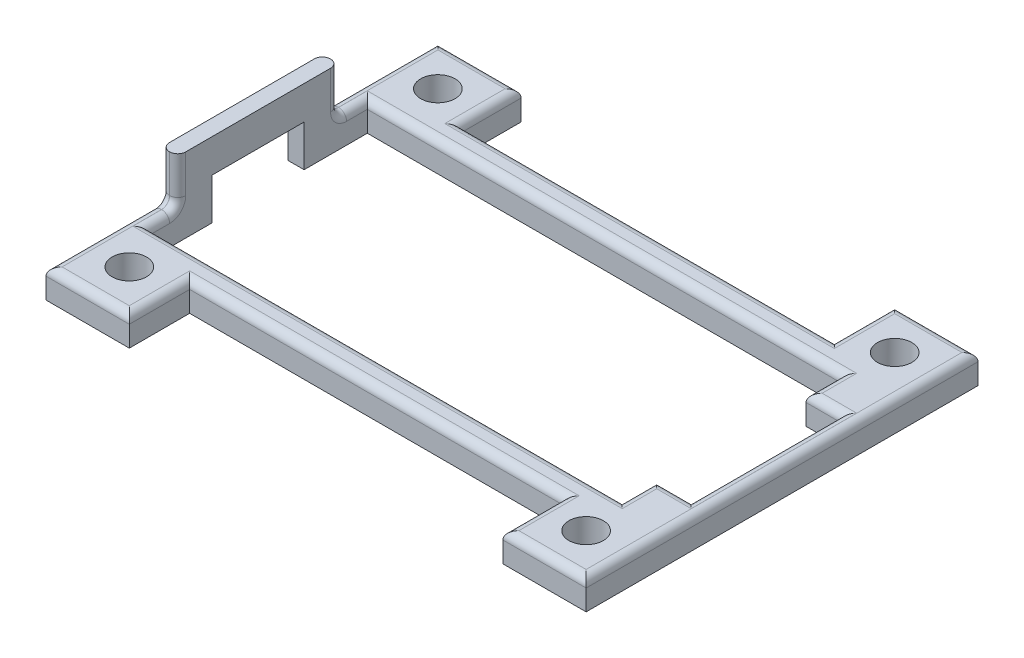
SolidWorks part; units mm, degrees
ref_plane "Front Plane" through (0, 0, 0) normal (0, 0, 1) x (1, 0, 0)
ref_plane "Top Plane" through (0, 0, 0) normal (0, 1, 0) x (1, 0, 0)
ref_plane "Right Plane" through (0, 0, 0) normal (1, 0, 0) x (0, 0, -1)
sketch "Sketch1" plane through (0, 0, 0) normal (0, 1, 0) x (1, 0, 0)
  line L1 (0, 0) -> (44.18, 0)
  line L2 (0, 0) -> (0, 19)
  line L3 (0, 19) -> (44.18, 19)
  line L4 (44.18, 0) -> (44.18, 19)
  line L5 (-1.41, 21.3) -> (45.59, 21.3)
  line L6 (-1.41, 21.3) -> (-1.41, -2.3)
  line L7 (-1.41, -2.3) -> (45.59, -2.3)
  line L8 (45.59, 21.3) -> (45.59, -2.3)
  point P9 (22.09, 21.3)
  point P10 (22.09, 19)
  point P11 (0, 9.5)
  point P12 (-1.41, 9.5)
  point P13 (22.09, 19)
  dimension "D1" = 19
  dimension "D2" = 44.18
  dimension "D3" = 47
  dimension "D4" = 23.6
extrude "Boss-Extrude1" add sketch "Sketch1" along normal blind 5.5
sketch "Sketch2" plane through (0, 5.5, 0) normal (0, 1, 0) x (1, 0, 0)
  line L1 (0, 19) -> (44.18, 19)
  line L2 (0, 19) -> (0, 0)
  line L3 (0, 0) -> (44.18, 0)
  line L4 (44.18, 19) -> (44.18, 0)
sketch "Sketch3" plane through (0, 0, 0) normal (0, -1, 0) x (1, 0, 0)
  line L1 (0, 0) -> (44.18, 0)
  line L2 (0, 0) -> (0, -19)
  line L3 (0, -19) -> (44.18, -19)
  line L4 (44.18, 0) -> (44.18, -19)
extrude "Boss-Extrude2" add sketch "Sketch3" against normal blind 3
sketch "Sketch6" plane through (0, 0, 2.3) normal (0, 0, 1) x (1, 0, 0)
  line L0 (-1.41, 0) -> (45.59, 0) construction
  line L1 (-1.41, 5.5) -> (5.84, 5.5)
  line L2 (-1.41, 5.5) -> (-1.41, 0)
  line L3 (-1.41, 0) -> (5.84, 0)
  line L4 (5.84, 5.5) -> (5.84, 0)
  line L6 (45.59, 5.5) -> (38.34, 5.5)
  line L7 (45.59, 5.5) -> (45.59, 0)
  line L8 (45.59, 0) -> (38.34, 0)
  line L9 (38.34, 5.5) -> (38.34, 0)
  dimension "D1" = 7.25
  dimension "D2" = 7.25
extrude "Boss-Extrude3" add sketch "Sketch6" along normal blind 5.25
sketch "Sketch7" plane through (0, 0, -21.3) normal (0, 0, -1) x (-1, 0, 0)
  line L0 (-45.59, 0) -> (1.41, 0) construction
  line L1 (-45.59, 5.5) -> (-38.34, 5.5)
  line L2 (-45.59, 5.5) -> (-45.59, 0)
  line L3 (-45.59, 0) -> (-38.34, 0)
  line L4 (-38.34, 5.5) -> (-38.34, 0)
  line L6 (1.41, 5.5) -> (-5.84, 5.5)
  line L7 (1.41, 5.5) -> (1.41, 0)
  line L8 (1.41, 0) -> (-5.84, 0)
  line L9 (-5.84, 5.5) -> (-5.84, 0)
  dimension "D1" = 7.25
  dimension "D2" = 7.25
extrude "Boss-Extrude4" add sketch "Sketch7" along normal blind 5.25
sketch "Sketch8" plane through (0, 5.5, 0) normal (0, 1, 0) x (1, 0, 0)
  line L0 (45.59, -7.55) -> (45.59, 26.55) construction
  line L1 (38.34, 26.55) -> (45.59, 26.55) construction
  line L2 (44.18, 9.5) -> (-13.9525, 9.5) construction
  line L3 (44.18, 0) -> (44.18, 19) construction
  line L4 (22.09, 0) -> (22.09, 19) construction
  line L5 (0, 0) -> (44.18, 0) construction
  line L6 (44.18, 19) -> (0, 19) construction
  circle A0 centre (41.965, 22.925) radius 1.5
  circle A1 centre (41.965, -3.925) radius 1.5
  circle A2 centre (2.215, -3.925) radius 1.5
  circle A3 centre (2.215, 22.925) radius 1.5
  point P4 (41.965, 26.55)
  dimension "D1" = 3
  dimension "D2" = 3.625
  dimension "D3" = 3.625
extrude "Cut-Extrude2" cut sketch "Sketch8" against normal through all
sketch "Sketch9" plane through (0, 0, 0) normal (0, -1, 0) x (1, 0, 0)
  line L1 (-2.6893, 8.6737) -> (49.0456, 8.6737)
  line L2 (-2.6893, 8.6737) -> (-2.6893, -28.0755)
  line L3 (-2.6893, -28.0755) -> (49.0456, -28.0755)
  line L4 (49.0456, 8.6737) -> (49.0456, -28.0755)
extrude "Cut-Extrude3" cut sketch "Sketch9" against normal blind 3
sketch "Sketch10" plane through (0, 5.5, 0) normal (0, 1, 0) x (1, 0, 0)
  line L0 (-1.41, 26.55) -> (-1.41, -7.55) construction
  line L1 (-1.41, 16.5) -> (0, 16.5)
  line L2 (-1.41, 16.5) -> (-1.41, 2.5)
  line L3 (-1.41, 2.5) -> (0, 2.5)
  line L4 (0, 16.5) -> (0, 2.5)
  line L5 (0, 19) -> (0, 0) construction
  point P8 (0, 9.5)
  point P9 (0, 9.5)
  dimension "D1" = 14
extrude "Boss-Extrude5" add sketch "Sketch10" along normal blind 4
sketch "Sketch11" plane through (44.18, 0, 0) normal (-1, 0, 0) x (0, 0, 1)
  line L0 (-19, 3) -> (0, 3) construction
  line L1 (-19, 5.5) -> (-16, 5.5)
  line L2 (-19, 5.5) -> (-19, 3)
  line L3 (-19, 3) -> (-16, 3)
  line L4 (-16, 5.5) -> (-16, 3)
  line L6 (0, 5.5) -> (-3, 5.5)
  line L7 (0, 5.5) -> (0, 3)
  line L8 (0, 3) -> (-3, 3)
  line L9 (-3, 5.5) -> (-3, 3)
  dimension "D1" = 3
  dimension "D2" = 3
extrude "Boss-Extrude6" add sketch "Sketch11" along normal blind 3
sketch "Sketch12" plane through (0, 3, 0) normal (0, -1, 0) x (1, 0, 0)
  line L0 (-1.41, 7.55) -> (-1.41, -26.55) construction
  line L1 (-1.41, -5.5) -> (0, -5.5)
  line L2 (-1.41, -5.5) -> (-1.41, -13.5)
  line L3 (-1.41, -13.5) -> (0, -13.5)
  line L4 (0, -5.5) -> (0, -13.5)
  line L5 (0, 0) -> (0, -19) construction
  line L6 (45.59, -26.55) -> (45.59, 7.55) construction
  point P8 (0, -9.5)
  point P9 (45.59, -9.5)
  dimension "D1" = 8
extrude "Cut-Extrude4" cut sketch "Sketch12" against normal blind 3.6
fillet "Fillet1" radius 0.7 28 edges at (2.215, 5.5, -26.55) (5.84, 5.5, -23.925) (41.965, 5.5, -26.55) (45.59, 5.5, -9.5) (41.965, 5.5, 7.55) (38.34, 5.5, 4.925) (2.215, 5.5, 7.55) (20.59, 5.5, 0) (41.18, 5.5, -1.5) (42.68, 5.5, -3) (44.18, 5.5, -9.5) (42.68, 5.5, -16) (41.18, 5.5, -17.5) (20.59, 5.5, -19)
